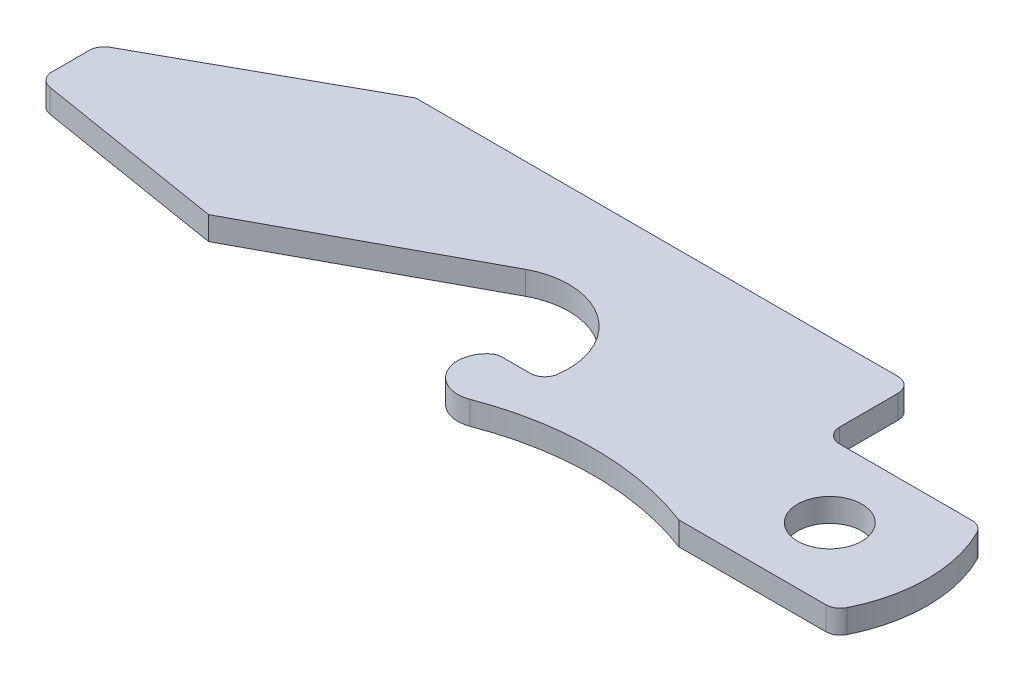
SolidWorks part; units mm, degrees
material "Stainless Steel (ferritic)"
ref_plane "Front Plane" through (0, 0, 0) normal (0, 0, 1) x (1, 0, 0)
ref_plane "Top Plane" through (0, 0, 0) normal (0, 1, 0) x (1, 0, 0)
ref_plane "Right Plane" through (0, 0, 0) normal (1, 0, 0) x (0, 0, -1)
sketch "Sketch1" plane through (0, 0, 0) normal (0, 1, 0) x (1, 0, 0)
  line L0 (0, 0) -> (0, -2.54)
  line L1 (0, -2.54) -> (8.774, -3.9713)
  line L2 (8.774, -3.9713) -> (17.7147, 0.8547)
  line L3 (37.2493, 1.1087) -> (30.48, 1.1087)
  line L4 (30.48, 1.1087) -> (30.48, 4.9187)
  line L5 (30.48, 4.9187) -> (8.89, 4.9187)
  line L6 (8.89, 4.9187) -> (0, 0)
  line L7 (22.2308, -2.9553) -> (20.32, -2.9553)
  line L8 (30.48, -5.2413) -> (37.2493, -5.2413)
  arc A0 (17.7147, 0.8547) -> (22.2308, -2.9553) centre (19.2228, -1.9393) cw
  arc A4 (37.2493, -5.2413) -> (37.2493, 1.1087) centre (31.75, -2.0663) ccw
  arc A5 (20.32, -2.9553) -> (21.4087, -5.2413) centre (20.9552, -4.0551) ccw
  arc A6 (21.4087, -5.2413) -> (30.48, -5.2413) centre (25.9444, -17.1038) cw
  circle A7 centre (33.8646, -2.0663) radius 1.397
  point P15 (38.1, -2.0663)
  point P19 (33.8646, 1.1087)
  point P23 (35.2616, -2.0663)
  dimension "D5" = 3.175
  dimension "D12" = 1.27
  dimension "D13" = 6.35
  dimension "D14" = 12.7
  dimension "D18" = 2.794
  dimension "D1" = 2.54
  dimension "D2" = 8.89
  dimension "D3" = 10.16
  dimension "D4" = 10.16
  dimension "D6" = 17.78
  dimension "D7" = 38.1
  dimension "D8" = 7.62
  dimension "D9" = 6.35
  dimension "D10" = 3.81
  dimension "D11" = 8.89
  dimension "D15" = 4.064
  dimension "D16" = 21.59
  dimension "D17" = 3.81
extrude "Boss-Extrude1" add sketch "Sketch1" along normal blind 1.016
fillet "Fillet1" radius 0.635 8 edges at (0, 0.508, 2.54) (0, 0.508, 0) (30.48, 0.508, -4.9187) (30.48, 0.508, -1.1087) (20.32, 0.508, 2.9553) (22.2308, 0.508, 2.9553) (37.2493, 0.508, -1.1087) (37.2493, 0.508, 5.2413)
ref_plane "Plane1" through (0, -0.8411, -0.1483) normal (0, -0.9848, -0.1736) x (-1, 0, 0)
sketch "Sketch3" plane through (0, -0.8411, -0.1483) normal (0, -0.9848, -0.1736) x (-1, 0, 0)
  line L0 (-17.78, 3.7504) -> (-8.89, 3.7504)
  line L1 (-29.845, 5.0204) -> (-8.89, 5.0204) construction
  arc A0 (-8.89, 3.7504) -> (-17.78, 3.7504) centre (-13.335, 11.4494) cw
  dimension "D3" = 8.89
  dimension "D1" = 8.89
  dimension "D2" = 1.27
extrude "Cut-Extrude1" cut sketch "Sketch3" against normal blind 0.381 draft 5
